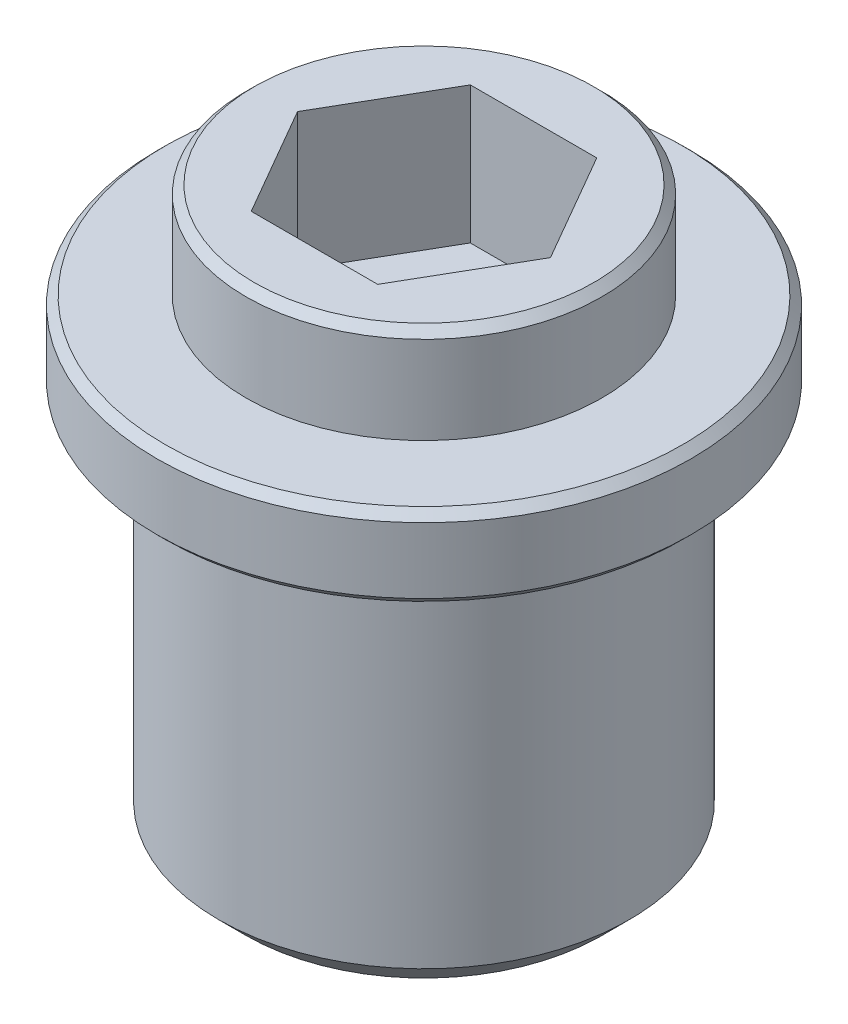
SolidWorks part; units mm, degrees
ref_plane "Plan de face" through (0, 0, 0) normal (0, 0, 1) x (1, 0, 0)
ref_plane "Plan de dessus" through (0, 0, 0) normal (0, 1, 0) x (1, 0, 0)
ref_plane "Plan de droite" through (0, 0, 0) normal (1, 0, 0) x (0, 0, -1)
sketch "Esquisse1" plane through (0, 0, 0) normal (0, 1, 0) x (1, 0, 0)
  circle A0 centre (0, 0) radius 7.5
  dimension "D1" = 15
extrude "Extrusion1" add sketch "Esquisse1" against normal blind 14
sketch "Esquisse2" plane through (0, 0, 0) normal (0, 1, 0) x (-1, 0, 0)
  circle A0 centre (0, 0) radius 9.75
  dimension "D1" = 19.5
extrude "Extrusion2" add sketch "Esquisse2" along normal blind 3
sketch "Esquisse3" plane through (0, 0, 0) normal (0, 1, 0) x (1, 0, 0)
  circle A0 centre (0, 0) radius 6.5
  dimension "D1" = 13
extrude "Extrusion3" add sketch "Esquisse3" along normal blind 6.5
sketch "Esquisse4" plane through (0, -14, 0) normal (0, -1, 0) x (1, 0, 0)
  circle A0 centre (0, 0) radius 4.5
  dimension "D1" = 9
extrude "Enlèv. mat.-Extru.1" cut sketch "Esquisse4" against normal blind 12.5
sketch "Esquisse5" plane through (0, 6.5, 0) normal (0, 1, 0) x (-1, 0, 0)
  line L1 (-4.6188, 0) -> (-2.3094, -4)
  line L2 (-2.3094, -4) -> (2.3094, -4)
  line L3 (2.3094, -4) -> (4.6188, 0)
  line L4 (4.6188, 0) -> (2.3094, 4)
  line L5 (2.3094, 4) -> (-2.3094, 4)
  line L6 (-2.3094, 4) -> (-4.6188, 0)
  circle A0 centre (0, 0) radius 4 construction
  dimension "D1" = 8
extrude "Enlèv. mat.-Extru.2" cut sketch "Esquisse5" against normal blind 5
chamfer "Chanfrein1" distance 1 angle 45 1 edges at (0, -14, 7.5)
chamfer "Chanfrein2" distance 0.3 angle 45 3 edges at (0, 6.5, 6.5) (0, 0, 9.75) (0, 3, 9.75)
